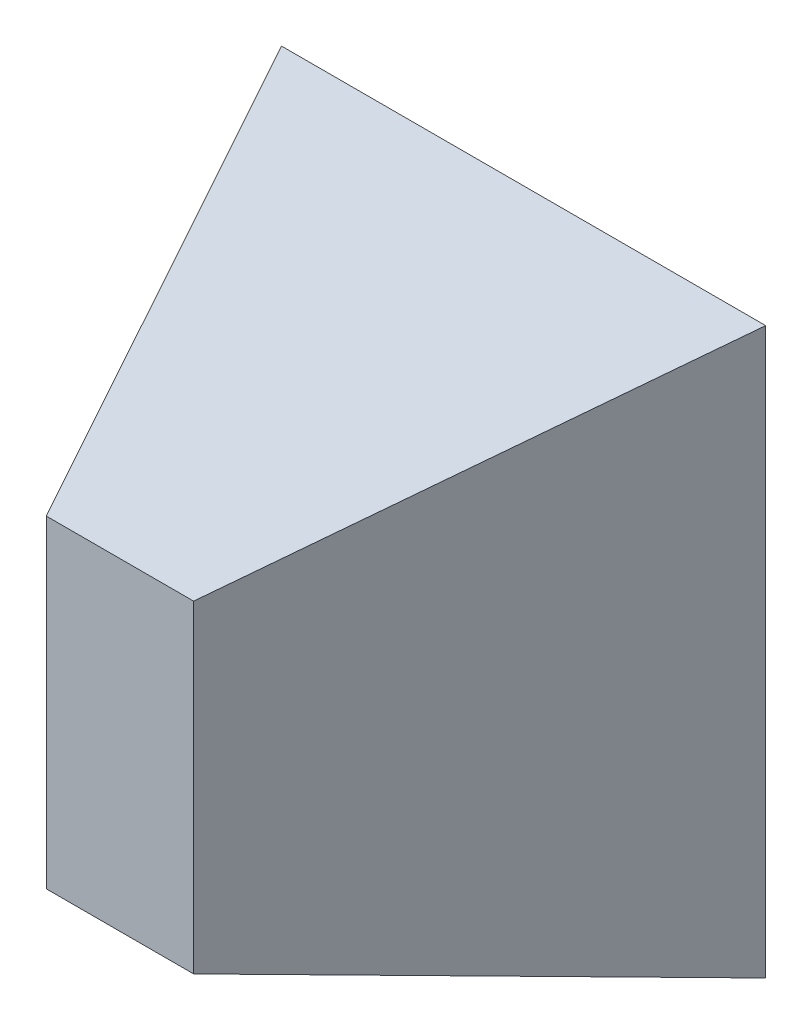
SolidWorks part; units mm, degrees
ref_plane "Front Plane" through (0, 0, 0) normal (0, 0, 1) x (1, 0, 0)
ref_plane "Top Plane" through (0, 0, 0) normal (0, 1, 0) x (1, 0, 0)
ref_plane "Right Plane" through (0, 0, 0) normal (1, 0, 0) x (0, 0, -1)
sketch "Sketch1" plane through (0, 0, 0) normal (0, 0, 1) x (1, 0, 0)
  line L1 (-152.4, -177.8) -> (152.4, -177.8)
  line L2 (-152.4, -177.8) -> (-152.4, 177.8)
  line L3 (-152.4, 177.8) -> (152.4, 177.8)
  line L4 (152.4, -177.8) -> (152.4, 177.8)
  line L5 (-152.4, -177.8) -> (152.4, 177.8) construction
  line L6 (-152.4, 177.8) -> (152.4, -177.8) construction
  point P0 (0, 0)
  dimension "D1" = 304.8
  dimension "D2" = 355.6
ref_plane "Plane1" through (0, 0, 254) normal (0, 0, 1) x (1, 0, 0)
sketch "Sketch2" plane through (0, 0, 254) normal (0, 0, 1) x (1, 0, 0)
  line L1 (-46.355, -101.6) -> (46.355, -101.6)
  line L2 (-46.355, -101.6) -> (-46.355, 101.6)
  line L3 (-46.355, 101.6) -> (46.355, 101.6)
  line L4 (46.355, -101.6) -> (46.355, 101.6)
  line L5 (-46.355, -101.6) -> (46.355, 101.6) construction
  line L6 (-46.355, 101.6) -> (46.355, -101.6) construction
  point P0 (0, 0)
  dimension "D1" = 92.71
  dimension "D2" = 203.2
loft "Loft1" add profiles "Sketch2", "Sketch1"
